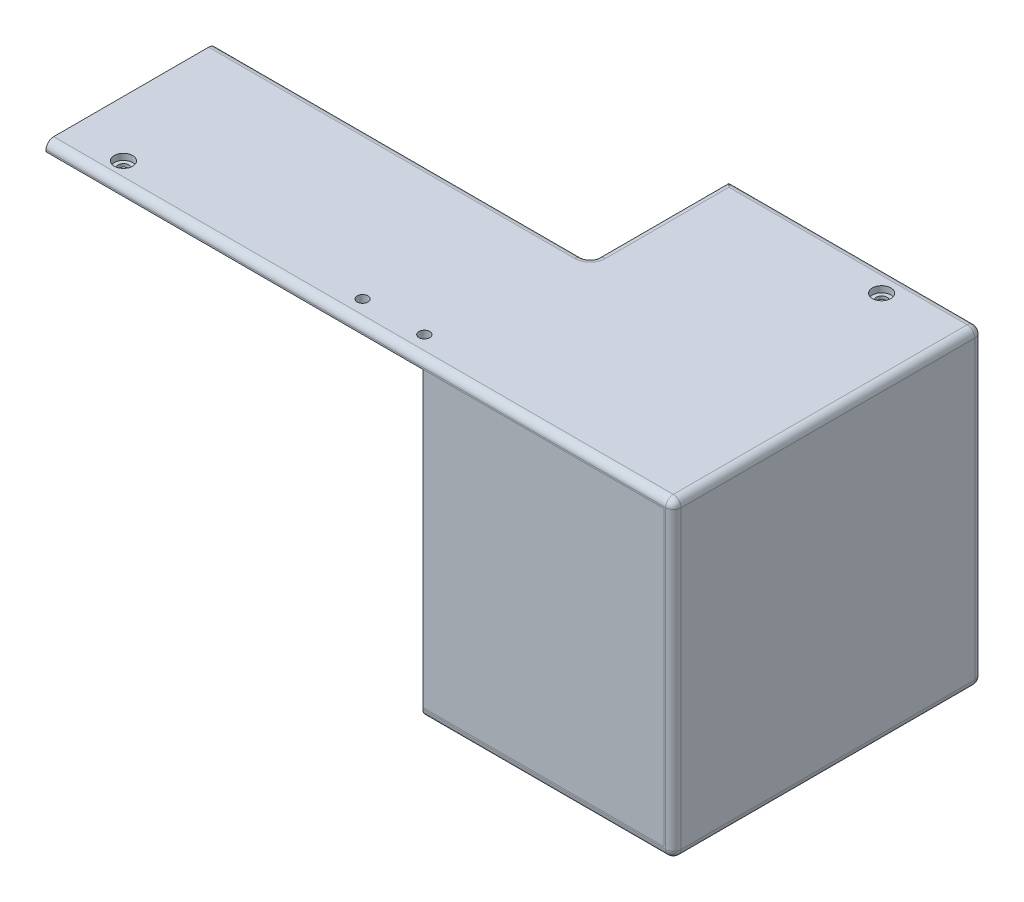
SolidWorks part; units mm, degrees
ref_plane "Front Plane" through (0, 0, 0) normal (0, 0, 1) x (1, 0, 0)
ref_plane "Top Plane" through (0, 0, 0) normal (0, 1, 0) x (1, 0, 0)
ref_plane "Right Plane" through (0, 0, 0) normal (1, 0, 0) x (0, 0, -1)
sketch "Sketch1" plane through (0, 0, 0) normal (0, 0, 1) x (1, 0, 0)
  line L0 (0, 0) -> (203.3, 0)
  line L1 (203.3, 0) -> (203.3, -100.9)
  line L3 (200.3, -97.9) -> (200.3, -3)
  line L4 (200.3, -3) -> (0, -3)
  line L5 (0, -3) -> (0, 0)
  line L6 (203.3, -100.9) -> (122.1, -100.9)
  line L7 (122.1, -100.9) -> (122.1, -97.9)
  line L8 (122.1, -97.9) -> (200.3, -97.9)
  dimension "D5" = 3
  dimension "D1" = 3
  dimension "D2" = 3
  dimension "D3" = 94.9
  dimension "D4" = 200.3
  dimension "D6" = 81.2
extrude "Main_Body" add sketch "Sketch1" along normal blind 100.2
sketch "Left_Screw_Holes" plane through (203.3, 0, 0) normal (1, 0, 0) x (0, 0, -1)
  line L1 (-100.2, 0) -> (0, 0) construction
  line L2 (0, -100.9) -> (0, 0) construction
  line L3 (-100.2, -100.9) -> (0, -100.9) construction
  line L4 (-7.5, -80.4) -> (-7.5, -17.5) construction
  circle A0 centre (-7.5, -17.5) radius 1.75
  circle A1 centre (-7.5, -80.4) radius 1.75
  dimension "D1" = 3.5
  dimension "D2" = 3.5
  dimension "D6" = 17.5
  dimension "D3" = 20.5
  dimension "D4" = 7.5
extrude "Right_Screw_Holes" [suppressed] cut sketch "Left_Screw_Holes" against normal blind 10
sketch "Sketch3" [suppressed] plane through (193.3, 0, 0) normal (1, 0, 0) x (0, 0, -1)
  circle A0 centre (-7.5, -17.5) radius 3
  circle A1 centre (-7.5, -80.4) radius 3
  dimension "D1" = 6
  dimension "D2" = 6
extrude "Right_Screw_Heads" [suppressed] cut sketch "Sketch3" against normal blind 2
sketch "Sketch4" plane through (0, 0, 0) normal (0, 1, 0) x (1, 0, 0)
  line L0 (178.1, -7.5) -> (18.1, -7.5) construction
  line L1 (203.3, 0) -> (0, 0) construction
  line L2 (203.3, -100.2) -> (203.3, 0) construction
  line L3 (18.1, -7.5) -> (10.3813, -7.4642) construction
  line L4 (18.1, -7.5) -> (18.1, -93.2) construction
  line L5 (18.1, -93.2) -> (18.1, -100.2) construction
  line L6 (203.3, -100.2) -> (0, -100.2) construction
  circle A1 centre (178.1, -7.5) radius 1.75
  circle A2 centre (18.1, -7.5) radius 1.75
  circle A3 centre (18.1, -93.2) radius 1.75
  dimension "D1" = 160
  dimension "D2" = 3.5
  dimension "D3" = 3.5
  dimension "D7" = 3.5
  dimension "D4" = 7.5
  dimension "D5" = 25.2
  dimension "D6" = 7
extrude "Back_Screw_Holes" cut sketch "Sketch4" against normal blind 3
sketch "Sketch5" plane through (0, 0, 0) normal (0, 1, 0) x (1, 0, 0)
  circle A0 centre (18.1, -7.5) radius 3
  circle A1 centre (178.1, -7.5) radius 3
  circle A2 centre (18.1, -93.2) radius 3
  dimension "D1" = 6
  dimension "D2" = 6
  dimension "D3" = 6
extrude "Back_Screw_Heads" cut sketch "Sketch5" against normal blind 2
sketch "Sketch7" plane through (0, -3, 0) normal (0, -1, 0) x (1, 0, 0)
  line L0 (0, 0) -> (200.3, 0) construction
  line L1 (-92.1202, 45) -> (121.1, 45)
  line L2 (-92.1202, 45) -> (-92.1202, 0)
  line L3 (-92.1202, 0) -> (121.1, 0)
  line L4 (121.1, 45) -> (121.1, 0)
  line L7 (203.3, 100.2) -> (203.3, 0) construction
  dimension "D1" = 45
  dimension "D3" = 82.2
extrude "Paper_Through_Hole" cut sketch "Sketch7" against normal blind 10
sketch "Sketch8" plane through (0, 0, 100.2) normal (0, 0, 1) x (1, 0, 0)
  line L1 (122.1, -97.9) -> (200.3, -97.9)
  line L2 (122.1, -97.9) -> (122.1, -3)
  line L3 (122.1, -3) -> (200.3, -3)
  line L4 (200.3, -97.9) -> (200.3, -3)
extrude "Top" add sketch "Sketch8" against normal blind 3 separate body
sketch "Sketch9" plane through (0, -100.9, 0) normal (0, -1, 0) x (1, 0, 0)
  line L0 (203.3, 100.2) -> (203.3, 0) construction
  line L1 (122.1, 0) -> (203.3, 0) construction
  circle A0 centre (178.1, 7.5) radius 1.75
  dimension "D1" = 3.5
  dimension "D2" = 25.2
  dimension "D3" = 7.5
extrude "Front_Right_Screw_Hole" cut sketch "Sketch9" against normal blind 3
sketch "Sketch11" plane through (0, -100.9, 0) normal (0, -1, 0) x (1, 0, 0)
  circle A0 centre (178.1, 7.5) radius 3
  dimension "D1" = 6
extrude "Front_Right_Screw_Head" cut sketch "Sketch11" against normal blind 2
sketch "Sketch19" plane through (0, -100.9, 0) normal (0, -1, 0) x (1, 0, 0)
  line L0 (132.1, 43) -> (122.1, 43) construction
  line L5 (122.1, 100.2) -> (122.1, 0) construction
  line L6 (122.1, 0) -> (203.3, 0) construction
  circle A0 centre (132.1, 43) radius 1.75
  dimension "D1" = 3.5
  dimension "D2" = 43
  dimension "D3" = 10
extrude "Latch_Screw_Hole" cut sketch "Sketch19" against normal blind 3
sketch "Sketch20" plane through (0, 0, 0) normal (0, 1, 0) x (1, 0, 0)
  line L0 (115.6, -100.2) -> (115.6, -93.2) construction
  line L1 (203.3, -100.2) -> (0, -100.2) construction
  line L2 (115.6, -93.2) -> (0, -93.2) construction
  line L3 (0, -100.2) -> (0, -45) construction
  line L4 (115.6, -93.2) -> (95.6, -93.2) construction
  line L5 (203.3, -100.2) -> (203.3, 0) construction
  circle A0 centre (95.6, -93.2) radius 1.75
  circle A1 centre (115.6, -93.2) radius 1.75
  dimension "D4" = 3.5
  dimension "D5" = 3.5
  dimension "D1" = 87.7
  dimension "D2" = 20
  dimension "D3" = 7
extrude "Cut-Extrude1" cut sketch "Sketch20" against normal blind 10
fillet "Fillet2" radius 2.5 11 edges at (203.3, 0, 50.1) (121.1, -1.5, 45) (121.1, 0, 22.5) (60.55, 0, 45) (101.65, 0, 100.2) (203.3, -50.45, 100.2) (162.7, -100.9, 100.2) (203.3, -100.9, 50.1) (162.7, -100.9, 0) (203.3, -50.45, 0) (162.2, 0, 0)
